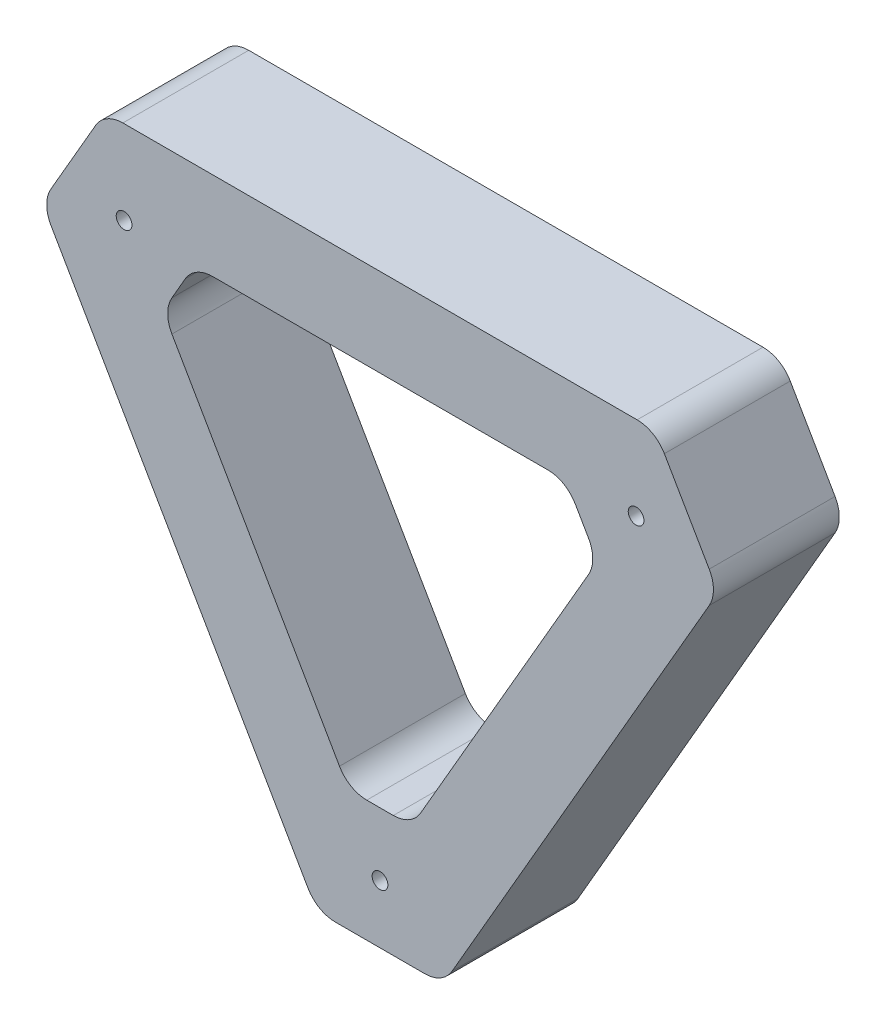
SolidWorks part; units mm, degrees
ref_plane "Plano frontal" through (0, 0, 0) normal (0, 0, 1) x (1, 0, 0)
ref_plane "Plano superior" through (0, 0, 0) normal (0, 1, 0) x (1, 0, 0)
ref_plane "Plano direito" through (0, 0, 0) normal (1, 0, 0) x (0, 0, -1)
sketch "Model" plane through (0, 0, 0) normal (0, 0, 1) x (1, 0, 0)
  line L0 (11.6949, 184.0077) -> (18.7988, 196.3107)
  line L1 (109.1831, 196.3193) -> (116.3092, 183.9973)
  line L2 (23.1285, 198.8105) -> (104.8545, 198.8162)
  line L3 (56.8791, 105.7136) -> (71.1053, 105.7136)
  line L4 (11.6943, 179.0083) -> (52.5485, 108.2145)
  line L5 (116.3107, 178.9937) -> (75.4352, 108.2132)
  line L6 (30.9268, 178.6517) -> (33.0412, 182.3135)
  line L7 (97.1295, 178.6724) -> (95.0148, 182.3291)
  line L8 (30.9258, 173.653) -> (57.5539, 127.4948)
  line L9 (61.8849, 124.9933) -> (66.1118, 124.9933)
  line L10 (70.4407, 127.4912) -> (97.1301, 173.6672)
  line L11 (90.6853, 184.826) -> (37.37, 184.8133)
  arc A0 (71.1053, 105.7136) -> (75.4352, 108.2132) centre (71.1053, 110.7136) ccw
  arc A1 (52.5485, 108.2145) -> (56.8791, 105.7136) centre (56.8791, 110.7136) ccw
  arc A2 (116.3107, 178.9937) -> (116.3092, 183.9973) centre (111.9808, 181.4941) ccw
  arc A3 (109.1831, 196.3193) -> (104.8545, 198.8162) centre (104.8548, 193.8162) ccw
  arc A4 (23.1285, 198.8105) -> (18.7988, 196.3107) centre (23.1288, 193.8105) ccw
  arc A5 (11.6949, 184.0077) -> (11.6943, 179.0083) centre (16.025, 181.5075) ccw
  arc A6 (57.5539, 127.4948) -> (61.8849, 124.9933) centre (61.8849, 129.9933) ccw
  arc A7 (66.1118, 124.9933) -> (70.4407, 127.4912) centre (66.1118, 129.9933) ccw
  arc A8 (97.1301, 173.6672) -> (97.1295, 178.6724) centre (92.8012, 176.1693) ccw
  arc A9 (95.0148, 182.3291) -> (90.6853, 184.826) centre (90.6865, 179.826) ccw
  arc A10 (37.37, 184.8133) -> (33.0412, 182.3135) centre (37.3712, 179.8133) ccw
  arc A11 (30.9268, 178.6517) -> (30.9258, 173.653) centre (35.2568, 176.1515) ccw
  circle A12 centre (23.3215, 185.4858) radius 1.25
  circle A13 centre (63.9917, 114.9804) radius 1.25
  circle A14 centre (104.6867, 185.4921) radius 1.25
  dimension "D1" = 81.3652
  dimension "D2" = 81.4124
  dimension "D3" = 14.2342
  dimension "D4" = 81.726
extrude "Ressalto-extrusão1" add sketch "Model" along normal blind 20
